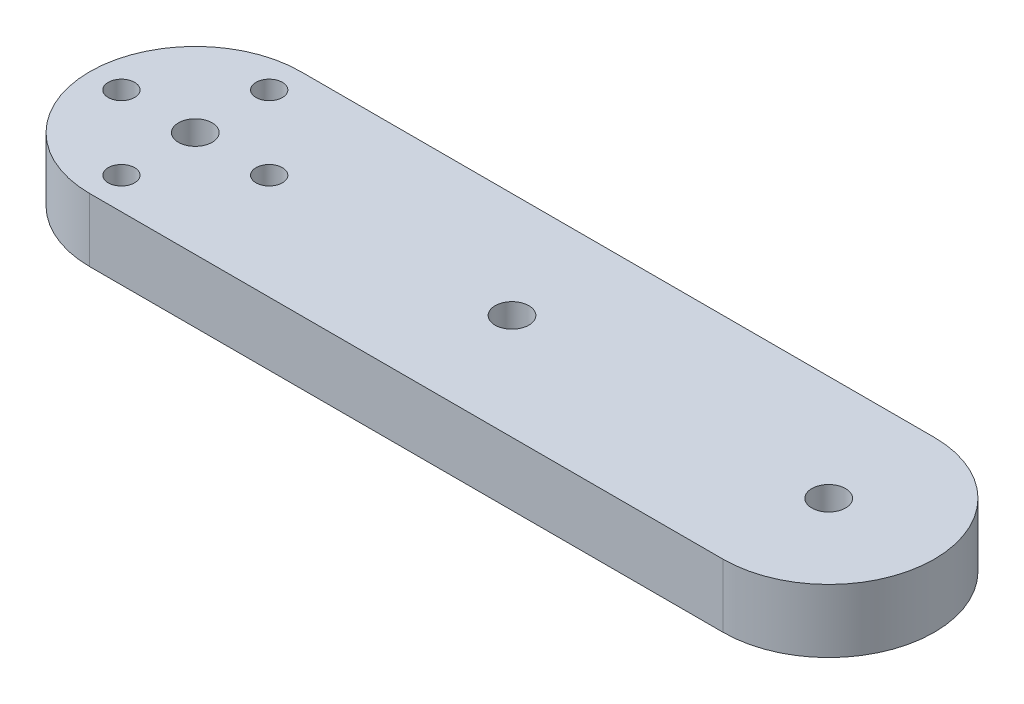
SolidWorks part; units mm, degrees
ref_plane "Front Plane" through (0, 0, 0) normal (0, 0, 1) x (1, 0, 0)
ref_plane "Top Plane" through (0, 0, 0) normal (0, 1, 0) x (1, 0, 0)
ref_plane "Right Plane" through (0, 0, 0) normal (1, 0, 0) x (0, 0, -1)
sketch "Sketch1" plane through (0, 0, 0) normal (0, 1, 0) x (1, 0, 0)
  line L0 (-30, 20) -> (-30, 0) construction
  line L1 (0, 0) -> (-60, 0)
  line L3 (0, 20) -> (-60, 20)
  line L5 (-60, 20) -> (-60, 0) construction
  line L6 (-70, 10) -> (-50, 10) construction
  line L7 (10, 10) -> (8.25, 10) construction
  line L8 (0, 20) -> (0, 18.25) construction
  line L9 (-8.25, 10) -> (-10, 10) construction
  line L10 (0, 15.75) -> (0, 4.25) construction
  line L11 (1.6, 10) -> (-5.75, 10) construction
  line L12 (0, 1.75) -> (0, 0) construction
  arc A0 (-60, 20) -> (-60, 0) centre (-60, 10) ccw
  arc A1 (0, 20) -> (0, 0) centre (0, 10) cw
  circle A2 centre (-60, 10) radius 1.6
  circle A3 centre (-60, 10) radius 10 construction
  circle A4 centre (0, 10) radius 10 construction
  circle A5 centre (-60, 17) radius 1.25
  circle A6 centre (-60, 3) radius 1.25
  circle A7 centre (-67, 10) radius 1.25
  circle A8 centre (-53, 10) radius 1.25
  circle A10 centre (0, 10) radius 1.6
  circle A14 centre (-30, 10) radius 1.6
  dimension "D3" = 20
  dimension "D4" = 3.2
  dimension "D5" = 2.5
  dimension "D7" = 2.5
  dimension "D9" = 3.2
  dimension "D1" = 60
  dimension "D2" = 20
  dimension "D6" = 7
  dimension "D8" = 7
extrude "Boss-Extrude1" add sketch "Sketch1" along normal blind 6
